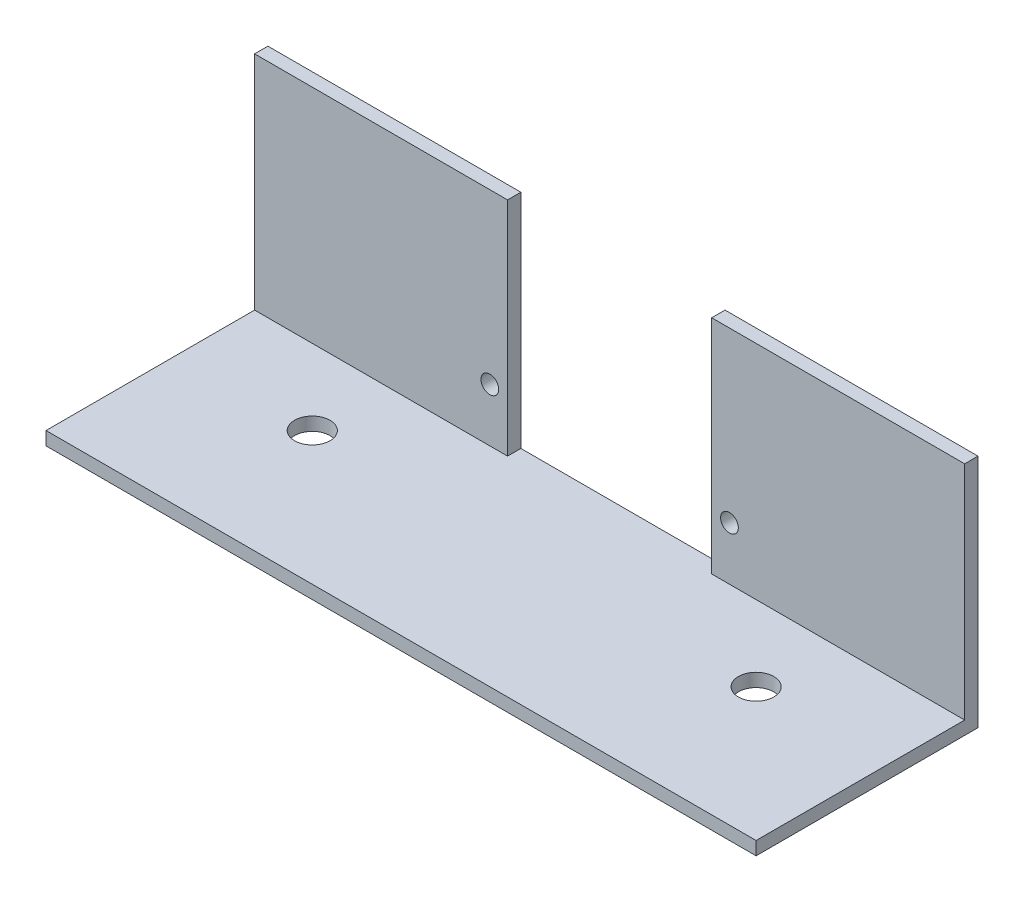
SolidWorks part; units mm, degrees
ref_plane "Front Plane" through (0, 0, 0) normal (0, 0, 1) x (1, 0, 0)
ref_plane "Top Plane" through (0, 0, 0) normal (0, 1, 0) x (1, 0, 0)
ref_plane "Right Plane" through (0, 0, 0) normal (1, 0, 0) x (0, 0, -1)
sketch "Sketch1" plane through (0, 0, 0) normal (0, 1, 0) x (1, 0, 0)
  line L0 (-25, -12.5) -> (-25, 2.5) construction
  line L1 (-40, 12.5) -> (40, 12.5)
  line L2 (-40, 12.5) -> (-40, -12.5)
  line L3 (-40, -12.5) -> (40, -12.5)
  line L4 (40, 12.5) -> (40, -12.5)
  line L5 (-40, 12.5) -> (40, -12.5) construction
  line L6 (-40, -12.5) -> (40, 12.5) construction
  line L7 (-25, 2.5) -> (25, 2.5) construction
  circle A0 centre (-25, 2.5) radius 2
  circle A1 centre (25, 2.5) radius 2
  point P0 (0, 0)
  point P6 (0, -12.5)
  point P7 (-25, -12.5)
  point P8 (25, -12.5)
  dimension "D4" = 4
  dimension "D5" = 4
  dimension "D1" = 25
  dimension "D2" = 25
  dimension "D3" = 50
  dimension "D6" = 25
  dimension "D7" = 80
  dimension "D8" = 15
extrude "Boss-Extrude1" add sketch "Sketch1" along normal blind 1.5
sketch "Sketch2" plane through (0, 1.5, 0) normal (0, 1, 0) x (1, 0, 0)
  line L0 (40, 12.5) -> (-40, 12.5) construction
  line L1 (-40, 12.5) -> (-11.5, 12.5)
  line L2 (-40, 12.5) -> (-40, 11)
  line L3 (-11.5, 12.5) -> (-11.5, 11)
  line L4 (-40, 11) -> (-11.5, 11)
  line L5 (11.5, 12.5) -> (40, 12.5)
  line L6 (11.5, 12.5) -> (11.5, 11)
  line L7 (40, 12.5) -> (40, 11)
  line L8 (11.5, 11) -> (40, 11)
  point P0 (11.5, 12.5)
  point P1 (-11.5, 12.5)
  point P6 (0, 12.5)
  dimension "D1" = 11.5
  dimension "D2" = 11.5
  dimension "D3" = 1.5
  dimension "D4" = 1.5
extrude "Boss-Extrude2" add sketch "Sketch2" along normal blind 25 contours L4 L3 L1 L2 | L8 L7 L5 L6
sketch "Sketch3" plane through (0, 0, -12.5) normal (0, 0, -1) x (-1, 0, 0)
  line L0 (0, 1.5) -> (0, 7.5) construction
  line L1 (-11.5, 1.5) -> (11.5, 1.5) construction
  line L2 (0, 7.5) -> (13.5, 7.5) construction
  circle A0 centre (13.5, 7.5) radius 1
  circle A1 centre (-13.5, 7.5) radius 1
  dimension "D3" = 2
  dimension "D1" = 6
  dimension "D2" = 13.5
extrude "Cut-Extrude1" cut sketch "Sketch3" against normal up to surface (1.5 mm away) up to face at (25.75, 14, -11)
